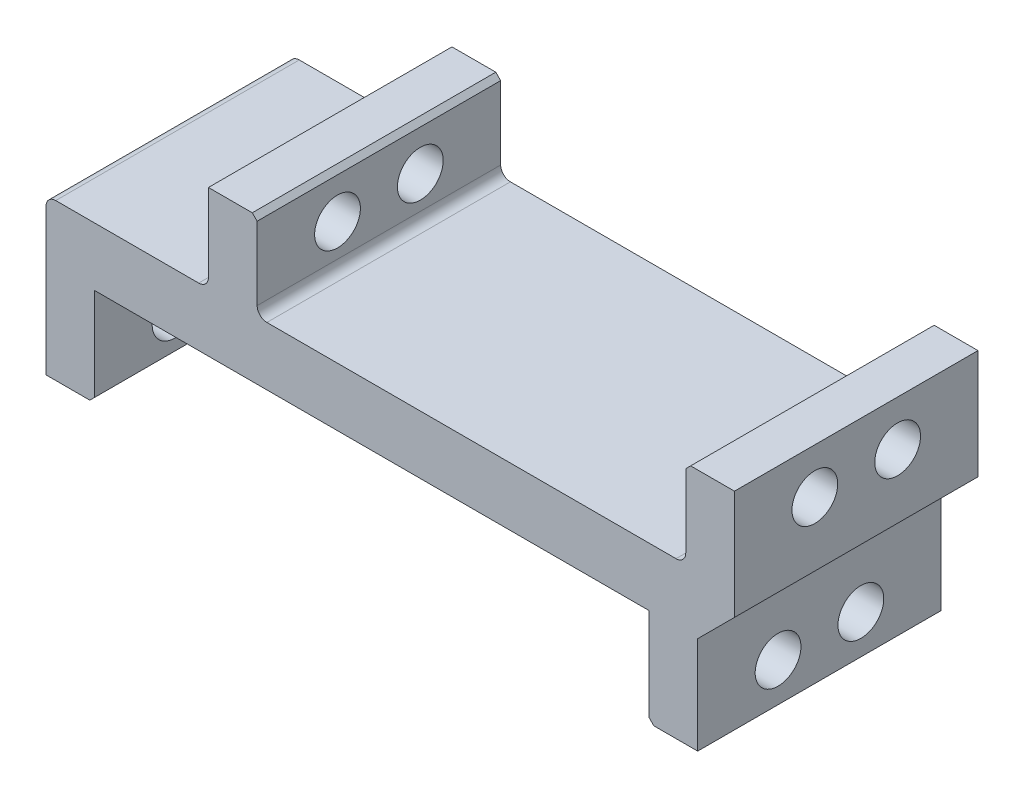
SolidWorks part; units mm, degrees
ref_plane "Front Plane" through (0, 0, 0) normal (0, 0, 1) x (1, 0, 0)
ref_plane "Top Plane" through (0, 0, 0) normal (0, 1, 0) x (1, 0, 0)
ref_plane "Right Plane" through (0, 0, 0) normal (1, 0, 0) x (0, 0, -1)
sketch "Sketch5" plane through (0, 0, 0) normal (0, 0, 1) x (1, 0, 0)
  line L1 (33.45, 0.7) -> (37.225, 4.475)
  line L2 (28.25, 0.5) -> (28.25, -43.5) construction
  line L3 (28.25, 0.5) -> (28.25, -43.5) construction
  line L4 (-28.25, 0.5) -> (28.25, 0.5) construction
  line L5 (-28.25, -43.5) -> (-28.25, 0.5) construction
  line L6 (-28.45, -9.3) -> (-28.45, 0.7)
  line L7 (-28.45, 0.7) -> (28.45, 0.7)
  line L8 (28.45, 0.7) -> (28.45, -9.3)
  line L9 (-28.45, -43.5) -> (-28.45, 0.7) construction
  line L10 (28.45, 0.7) -> (28.45, -43.5) construction
  line L11 (0, 0.7) -> (0, -43.5) construction
  line L12 (-27.75, 0.5) -> (27.75, 0.5) construction
  line L13 (-28.45, -9.3) -> (-33.45, -9.3)
  line L14 (28.45, -9.3) -> (33.45, -9.3)
  line L15 (-33.45, -9.3) -> (-33.45, 5.7)
  line L16 (33.45, -9.3) -> (33.45, 0.7)
  line L17 (-32.45, 6.7) -> (-17.775, 6.7)
  line L19 (-16.775, 7.7) -> (-16.775, 15.7)
  line L20 (37.225, 4.475) -> (37.225, 15.7)
  line L21 (-16.775, 15.7) -> (-11.775, 15.7)
  line L22 (37.225, 15.7) -> (32.225, 15.7)
  line L23 (-11.775, 15.7) -> (-11.775, 7.7)
  line L24 (32.225, 15.7) -> (32.225, 7.7)
  line L25 (-10.775, 6.7) -> (31.225, 6.7)
  line L26 (10.225, -75) -> (10.225, -48.5) construction
  line L27 (-11.775, 11.7) -> (32.225, 11.7) construction
  line L28 (-28.25, -43.5) -> (-28.25, 0) construction
  line L29 (28.25, 0) -> (28.25, -43.5) construction
  arc A0 (-11.775, 7.7) -> (-10.775, 6.7) centre (-10.775, 7.7) ccw
  arc A1 (32.225, 7.7) -> (31.225, 6.7) centre (31.225, 7.7) cw
  arc A4 (-17.775, 6.7) -> (-16.775, 7.7) centre (-17.775, 7.7) ccw
  arc A5 (-33.45, 5.7) -> (-32.45, 6.7) centre (-32.45, 5.7) cw
  point P7 (0, 0)
  point P16 (37.225, 4.7294)
  point P22 (0, 0)
  point P31 (-11.775, 6.7)
  point P34 (10.225, 11.7)
  point P35 (0, 0)
  point P43 (0, 0)
  point P46 (-33.45, 6.7)
  point P50 (0, 0)
  point P51 (0, -43.5)
  point P54 (0, 0)
  point P58 (0, 0)
  point P59 (0, 0)
  point P60 (28.45, -43.5)
  dimension "D7" = 1
  dimension "D2" = 10
  dimension "D3" = 5
  dimension "D4" = 5
  dimension "D5" = 44
  dimension "D6" = 6
  dimension "D8" = 9
  dimension "D9" = 45
  dimension "D1" = 0.2
extrude "Boss-Extrude3" add sketch "Sketch5" along normal mid plane 25
sketch "Sketch6" plane through (0, 0, 0) normal (1, 0, 0) x (0, 0, -1)
  line L1 (-4.25, 11.05) -> (4.25, 11.05) construction
  line L2 (-4.25, 11.05) -> (-4.25, -5.3) construction
  line L3 (-4.25, -5.3) -> (4.25, -5.3) construction
  line L4 (4.25, 11.05) -> (4.25, -5.3) construction
  line L5 (-4.25, 11.05) -> (4.25, -5.3) construction
  line L6 (-4.25, -5.3) -> (4.25, 11.05) construction
  line L9 (-12.5, -9.3) -> (12.5, -9.3) construction
  line L13 (-12.5, 6.7) -> (12.5, 6.7) construction
  circle A0 centre (-4.25, 11.05) radius 2.35
  circle A1 centre (4.25, 11.05) radius 2.35
  circle A2 centre (4.25, -5.3) radius 2.35
  circle A3 centre (-4.25, -5.3) radius 2.35
  point P10 (0, 2.875)
  dimension "D1" = 4.7
  dimension "D4" = 2
  dimension "D2" = 8.5
  dimension "D3" = 4
extrude "Cut-Extrude1" cut sketch "Sketch6" against normal through all both and the other way through all
chamfer "Chamfer1" distance 0.5 angle 45 4 edges at (32.225, 15.7, 0) (-11.775, 15.7, 0) (28.45, -9.3, 0) (-28.45, -9.3, 0)
